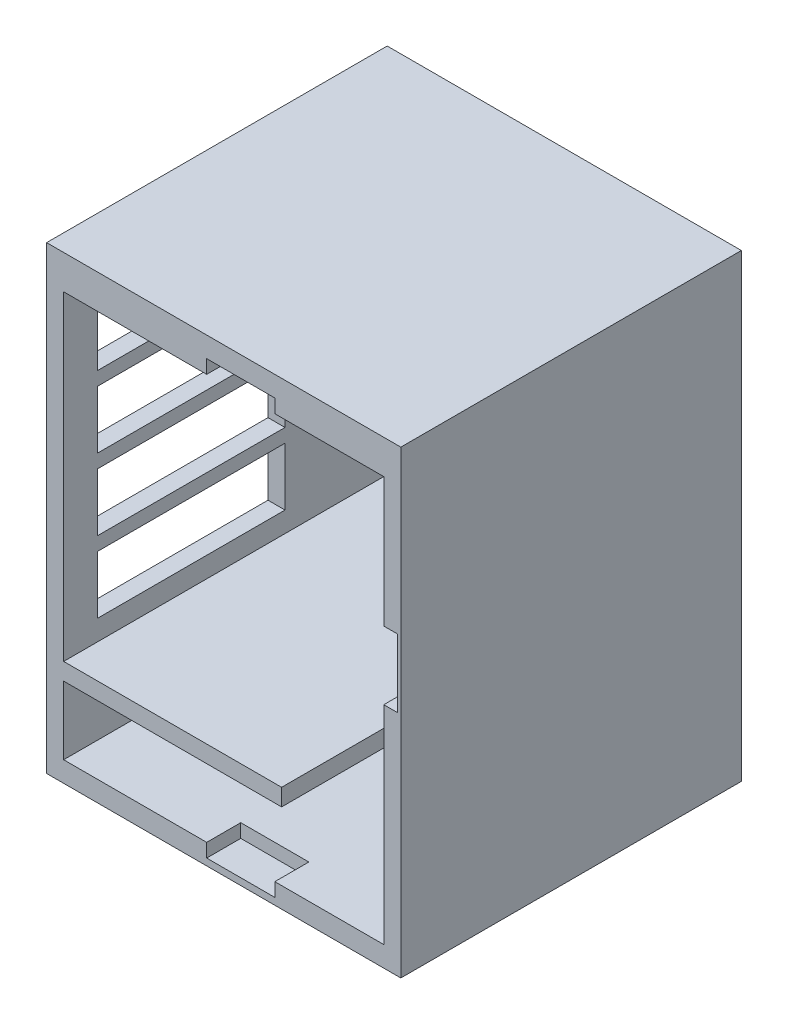
SolidWorks part; units mm, degrees
ref_plane "前基準面" through (0, 0, 0) normal (0, 0, 1) x (1, 0, 0)
ref_plane "上基準面" through (0, 0, 0) normal (0, 1, 0) x (1, 0, 0)
ref_plane "右基準面" through (0, 0, 0) normal (1, 0, 0) x (0, 0, -1)
sketch "草圖1" plane through (0, 0, 0) normal (0, 0, 1) x (1, 0, 0)
  line L5 (-72.8941, 49.2863) -> (31.1059, 49.2863)
  line L6 (-72.8941, 49.2863) -> (-72.8941, -85.7137)
  line L7 (-72.8941, -85.7137) -> (31.1059, -85.7137)
  line L8 (31.1059, 49.2863) -> (31.1059, -85.7137)
  circle A0 centre (-20.8941, -7.7137) radius 47
  dimension "D1" = 94
  dimension "D2" = 52
  dimension "D3" = 104
  dimension "D4" = 135
extrude "填料-伸長2" add sketch "草圖1" along normal blind 100
sketch "草圖2" plane through (0, 0, 100) normal (0, 0, 1) x (1, 0, 0)
  line L0 (31.1059, 49.2863) -> (-72.8941, 49.2863) construction
  line L1 (-67.8941, 39.2863) -> (26.1059, 39.2863)
  line L2 (-67.8941, 39.2863) -> (-67.8941, -54.7137)
  line L3 (-67.8941, -54.7137) -> (26.1059, -54.7137)
  line L4 (26.1059, 39.2863) -> (26.1059, -54.7137)
  line L5 (31.1059, -85.7137) -> (31.1059, 49.2863) construction
  dimension "D1" = 94
  dimension "D2" = 94
  dimension "D3" = 10
  dimension "D4" = 5
extrude "除料-伸長1" cut sketch "草圖2" against normal blind 95
sketch "草圖3" plane through (0, 0, 100) normal (0, 0, 1) x (1, 0, 0)
  line L1 (-67.8941, -59.7137) -> (26.1059, -59.7137)
  line L2 (-67.8941, -59.7137) -> (-67.8941, -79.7137)
  line L3 (-67.8941, -79.7137) -> (26.1059, -79.7137)
  line L4 (26.1059, -59.7137) -> (26.1059, -79.7137)
  line L5 (-72.8941, 49.2863) -> (-72.8941, -85.7137) construction
  line L6 (-67.8941, -54.7137) -> (26.1059, -54.7137) construction
  line L8 (26.1059, -59.7137) -> (-3.8941, -59.7137)
  line L9 (26.1059, -59.7137) -> (26.1059, -54.7137)
  line L10 (26.1059, -54.7137) -> (-3.8941, -54.7137)
  line L11 (-3.8941, -59.7137) -> (-3.8941, -54.7137)
  line M5 (26.1059, -54.7137) -> (-67.8941, -54.7137)
  dimension "D4" = 30
  dimension "D1" = 94
  dimension "D2" = 5
  dimension "D3" = 5
  dimension "D5" = 20
extrude "除料-伸長3" cut sketch "草圖3" against normal blind 70 contours L11 L1 L9 M5 | L4 L1 L2 L3
sketch "草圖4" plane through (0, 0, 100) normal (0, 0, 1) x (1, 0, 0)
  line L0 (31.1059, 49.2863) -> (-72.8941, 49.2863) construction
  line L1 (-67.8941, -79.7137) -> (26.1059, -79.7137) construction
  line L2 (-5.8941, -79.7137) -> (-25.8941, -79.7137)
  line L3 (-5.8941, -79.7137) -> (-5.8941, -83.7137)
  line L4 (-5.8941, -83.7137) -> (-25.8941, -83.7137)
  line L5 (-25.8941, -79.7137) -> (-25.8941, -83.7137)
  line L6 (-72.8941, 49.2863) -> (-72.8941, -85.7137) construction
  line L8 (26.1059, -79.7137) -> (26.1059, 39.2863) construction
  line L9 (26.1059, -18.7137) -> (30.1059, -18.7137)
  line L10 (26.1059, -18.7137) -> (26.1059, 1.2863)
  line L11 (26.1059, 1.2863) -> (30.1059, 1.2863)
  line L12 (30.1059, -18.7137) -> (30.1059, 1.2863)
  line L18 (26.1059, 39.2863) -> (-67.8941, 39.2863) construction
  line L19 (-5.8941, 39.2863) -> (-25.8941, 39.2863)
  line L20 (-5.8941, 39.2863) -> (-5.8941, 43.2863)
  line L21 (-5.8941, 43.2863) -> (-25.8941, 43.2863)
  line L22 (-25.8941, 39.2863) -> (-25.8941, 43.2863)
  line L24 (-72.8941, -85.7137) -> (31.1059, -85.7137) construction
  dimension "D1" = 20
  dimension "D2" = 47
  dimension "D3" = 4
  dimension "D4" = 4
  dimension "D5" = 4
  dimension "D7" = 67
  dimension "D8" = 20
extrude "除料-伸長4" cut sketch "草圖4" against normal blind 10
sketch "草圖6" plane through (-72.8941, 0, 0) normal (-1, 0, 0) x (0, 0, 1)
  line L20 (0, 49.2863) -> (0, -85.7137) construction
  line L21 (90, 31.2863) -> (35, 31.2863)
  line L22 (90, 31.2863) -> (90, 14.2863)
  line L23 (90, 14.2863) -> (35, 14.2863)
  line L24 (35, 31.2863) -> (35, 14.2863)
  line L25 (100, 49.2863) -> (0, 49.2863) construction
  line L27 (90, 10.2863) -> (35, 10.2863)
  line L28 (90, 10.2863) -> (90, -6.7137)
  line L29 (90, -6.7137) -> (35, -6.7137)
  line L30 (35, 10.2863) -> (35, -6.7137)
  line L31 (90, -10.7137) -> (35, -10.7137)
  line L32 (90, -10.7137) -> (90, -27.7137)
  line L33 (90, -27.7137) -> (35, -27.7137)
  line L34 (35, -10.7137) -> (35, -27.7137)
  line L35 (90, -31.7137) -> (35, -31.7137)
  line L36 (90, -31.7137) -> (90, -48.7137)
  line L37 (90, -48.7137) -> (35, -48.7137)
  line L38 (35, -31.7137) -> (35, -48.7137)
  dimension "D1" = 17
  dimension "D2" = 55
  dimension "D3" = 35
  dimension "D4" = 18
  dimension "D5" = 17
  dimension "D6" = 17
  dimension "D7" = 17
  dimension "D8" = 4
  dimension "D9" = 4
  dimension "D10" = 4
extrude "除料-伸長6" cut sketch "草圖6" against normal up to next
sketch "草圖7" plane through (0, -85.7137, 0) normal (0, -1, 0) x (1, 0, 0)
  line L0 (31.1059, 100) -> (31.1059, 0) construction
  line L1 (11.1059, 43) -> (-0.8941, 43)
  line L2 (11.1059, 43) -> (11.1059, 55)
  line L3 (11.1059, 55) -> (-0.8941, 55)
  line L4 (-0.8941, 43) -> (-0.8941, 55)
  line L5 (-72.8941, 100) -> (31.1059, 100) construction
  line L6 (-72.8941, 100) -> (-72.8941, 0) construction
  line L7 (-52.8941, 43) -> (-40.8941, 43)
  line L8 (-52.8941, 43) -> (-52.8941, 55)
  line L9 (-52.8941, 55) -> (-40.8941, 55)
  line L10 (-40.8941, 43) -> (-40.8941, 55)
  dimension "D1" = 12
  dimension "D2" = 12
  dimension "D3" = 20
  dimension "D4" = 45
  dimension "D5" = 20
  dimension "12" = 12
  dimension "D7" = 12
  dimension "D8" = 45
extrude "除料-伸長7" cut sketch "草圖7" against normal up to next
